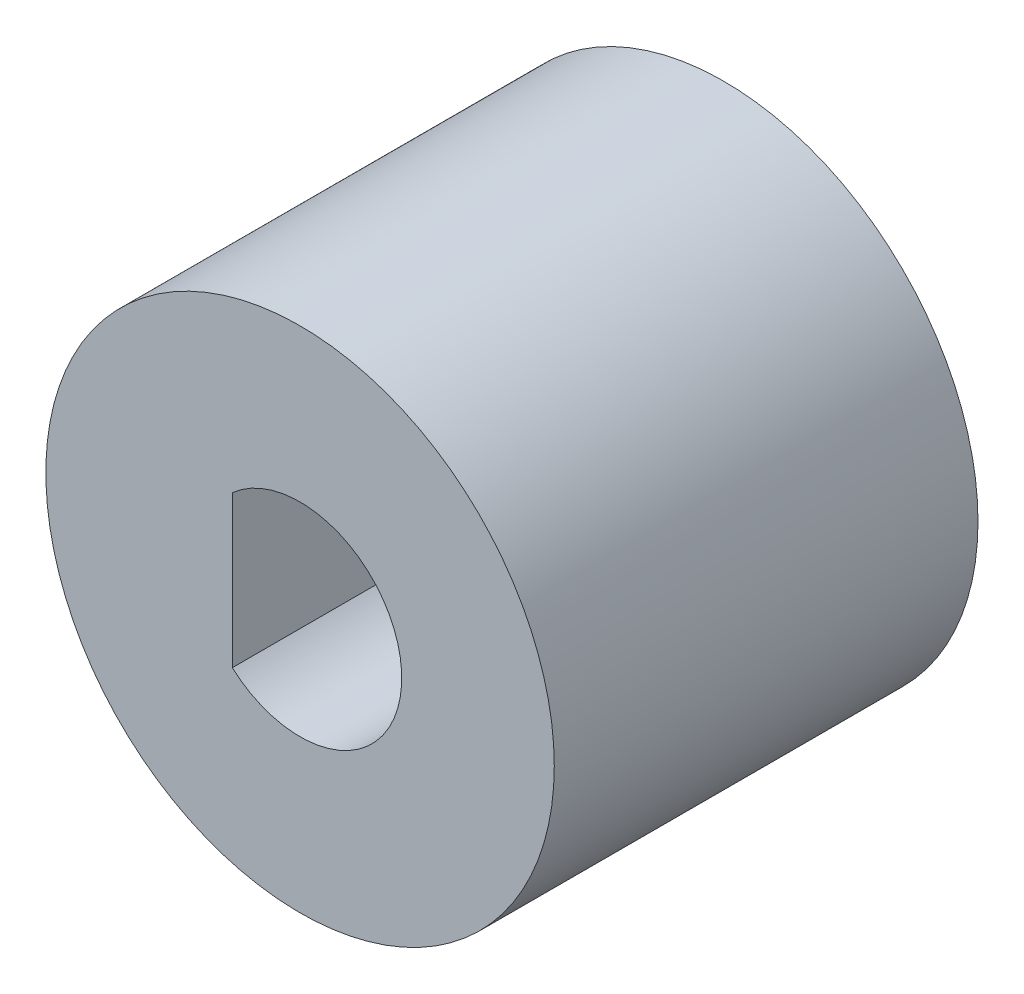
SolidWorks part; units mm, degrees
ref_plane "Plan de face" through (0, 0, 0) normal (0, 0, 1) x (1, 0, 0)
ref_plane "Plan de dessus" through (0, 0, 0) normal (0, 1, 0) x (1, 0, 0)
ref_plane "Plan de droite" through (0, 0, 0) normal (1, 0, 0) x (0, 0, -1)
sketch "Esquisse2" plane through (0, 0, 0) normal (0, 0, 1) x (1, 0, 0)
  line L0 (0, 0) -> (0, 15)
  line L1 (-4, 14.4568) -> (-4, -14.4568)
  circle A0 centre (0, 0) radius 15
  circle A1 centre (0, 0) radius 6
  dimension "D1" = 30
  dimension "D2" = 12
  dimension "D3" = 4
extrude "Boss.-Extru.1" add sketch "Esquisse2" along normal blind 25 contours A1 L1 A0 L0 | A1 L0 A0 L1 | A1 L1 A0 | L1 A1
